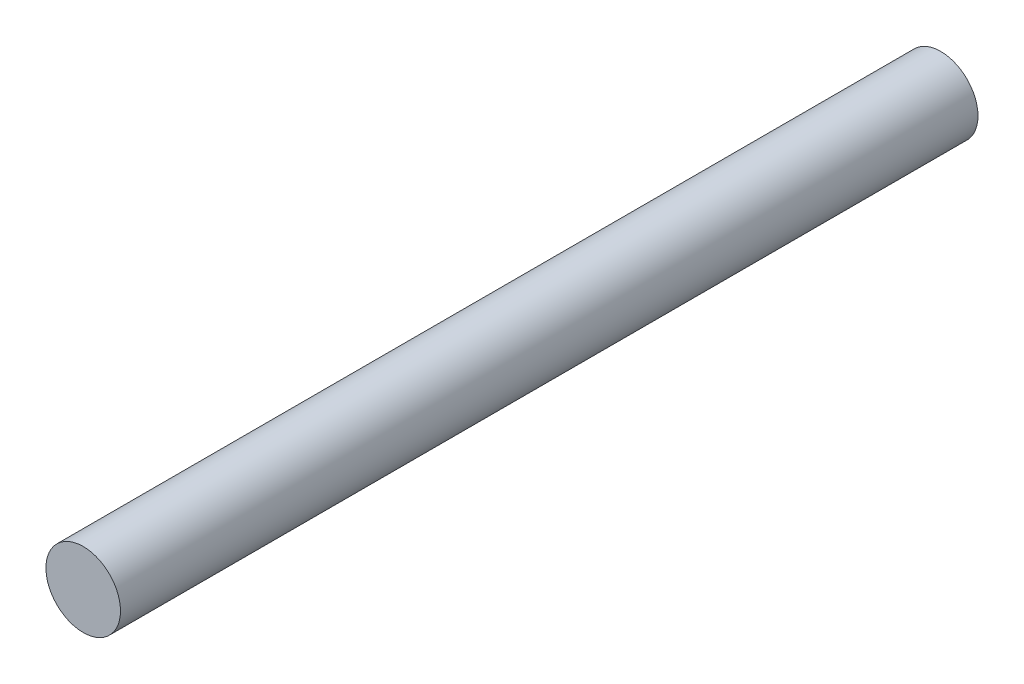
SolidWorks part; units mm, degrees
ref_plane "Front Plane" through (0, 0, 0) normal (0, 0, 1) x (1, 0, 0)
ref_plane "Top Plane" through (0, 0, 0) normal (0, 1, 0) x (1, 0, 0)
ref_plane "Right Plane" through (0, 0, 0) normal (1, 0, 0) x (0, 0, -1)
sketch "Sketch1" plane through (0, 0, 0) normal (0, 0, 1) x (1, 0, 0)
  circle A0 centre (0, 0) radius 1
  dimension "D1" = 2
extrude "Boss-Extrude1" add sketch "Sketch1" along normal blind 23
ref_plane "Plane1" through (0, 0, 11.5) normal (0, 0, 1) x (1, 0, 0)
